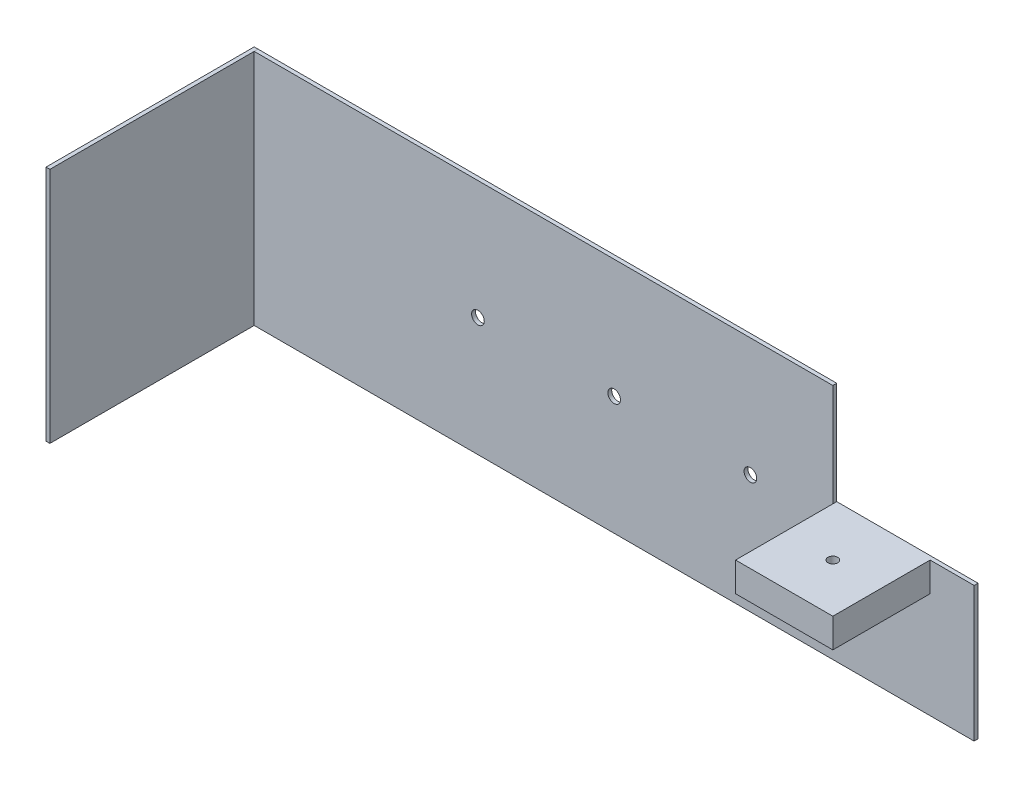
SolidWorks part; units mm, degrees
ref_plane "前视基准面" through (0, 0, 0) normal (0, 0, 1) x (1, 0, 0)
ref_plane "上视基准面" through (0, 0, 0) normal (0, 1, 0) x (1, 0, 0)
ref_plane "右视基准面" through (0, 0, 0) normal (1, 0, 0) x (0, 0, -1)
sketch "草图1" plane through (0, 0, 0) normal (0, 0, 1) x (1, 0, 0)
  line L1 (-185, 61) -> (185, 61)
  line L2 (-185, 61) -> (-185, -61)
  line L3 (-185, -61) -> (185, -61)
  line L4 (185, 61) -> (185, -61)
  line L5 (-185, 61) -> (185, -61) construction
  line L6 (-185, -61) -> (185, 61) construction
  point P0 (0, 0)
  dimension "D1" = 122
  dimension "D2" = 370
extrude "凸台-拉伸1" add sketch "草图1" along normal blind 2
sketch "草图2" plane through (0, 0, 2) normal (0, 0, 1) x (1, 0, 0)
  line L1 (-185, 61) -> (-187, 61)
  line L2 (-185, 61) -> (-185, -61)
  line L3 (-185, -61) -> (-187, -61)
  line L4 (-187, 61) -> (-187, -61)
  dimension "D1" = 122
  dimension "D2" = 2
extrude "凸台-拉伸2" add sketch "草图2" along normal blind 105 and the other way blind 2 separate body
sketch "草图3" plane through (0, 0, 2) normal (0, 0, 1) x (1, 0, 0)
  line L0 (-185, -61) -> (185, -61) construction
  line L1 (112.4, 8.3) -> (162.4, 8.3)
  line L2 (112.4, 8.3) -> (112.4, -6.7)
  line L3 (112.4, -6.7) -> (162.4, -6.7)
  line L4 (162.4, 8.3) -> (162.4, -6.7)
  line L5 (112.4, 8.3) -> (162.4, -6.7) construction
  line L6 (112.4, -6.7) -> (162.4, 8.3) construction
  line L7 (-185, 61) -> (-185, -61) construction
  point P0 (137.4, 0.8)
  dimension "D1" = 61.8
  dimension "D2" = 15
  dimension "D3" = 50
  dimension "D4" = 322.4
extrude "凸台-拉伸3" add sketch "草图3" along normal blind 50
sketch "草图4" plane through (0, 8.3, 0) normal (0, 1, 0) x (1, 0, 0)
  line L0 (112.4, -52) -> (112.4, -2) construction
  line L1 (162.4, -52) -> (112.4, -52) construction
  point P0 (137.4, -27)
  dimension "D1" = 25
  dimension "D2" = 25
hole_wizard "M6 螺纹孔1" positions "3D草图1" profile "草图5" tap size "M6" standard "GB" end condition up to next
sketch3d "3D草图1"
  point P0 (137.4, 8.3, 27)
sketch "草图5" plane through (137.4, 8.3, 27) normal (1, 0, 0) x (0, 0, 1)
  line L0 (0, 0) -> (0, 15.001)
  line L1 (0, 15.001) -> (2.5, 15.001)
  line L2 (2.5, 15.001) -> (2.5, 0)
  line L5 (2.5, 0) -> (0, 0)
  line L11 (0, -6.35) -> (0, 107.95) construction
  dimension "通孔螺纹孔钻头直径" = 5
  dimension "通孔螺纹孔钻头深度" = 15.001
cosmetic thread "孔螺蚊线1" parameters "D2"=6
sketch "草图6" plane through (0, 0, 2) normal (0, 0, 1) x (1, 0, 0)
  line L1 (185, 61) -> (112.4, 61)
  line L2 (185, 61) -> (185, 8.3)
  line L3 (185, 8.3) -> (112.4, 8.3)
  line L4 (112.4, 61) -> (112.4, 8.3)
extrude "切除-拉伸1" cut sketch "草图6" against normal blind 2
sketch "草图7" plane through (0, 0, 2) normal (0, 0, 1) x (1, 0, 0)
  circle A0 centre (-70, 0) radius 3.25
  circle A1 centre (0, 0) radius 3.25
  circle A2 centre (70, 0) radius 3.25
  dimension "D1" = 6.5
  dimension "D2" = 6.5
  dimension "D3" = 6.5
  dimension "D4" = 70
  dimension "D5" = 70
extrude "切除-拉伸2" cut sketch "草图7" against normal blind 2
